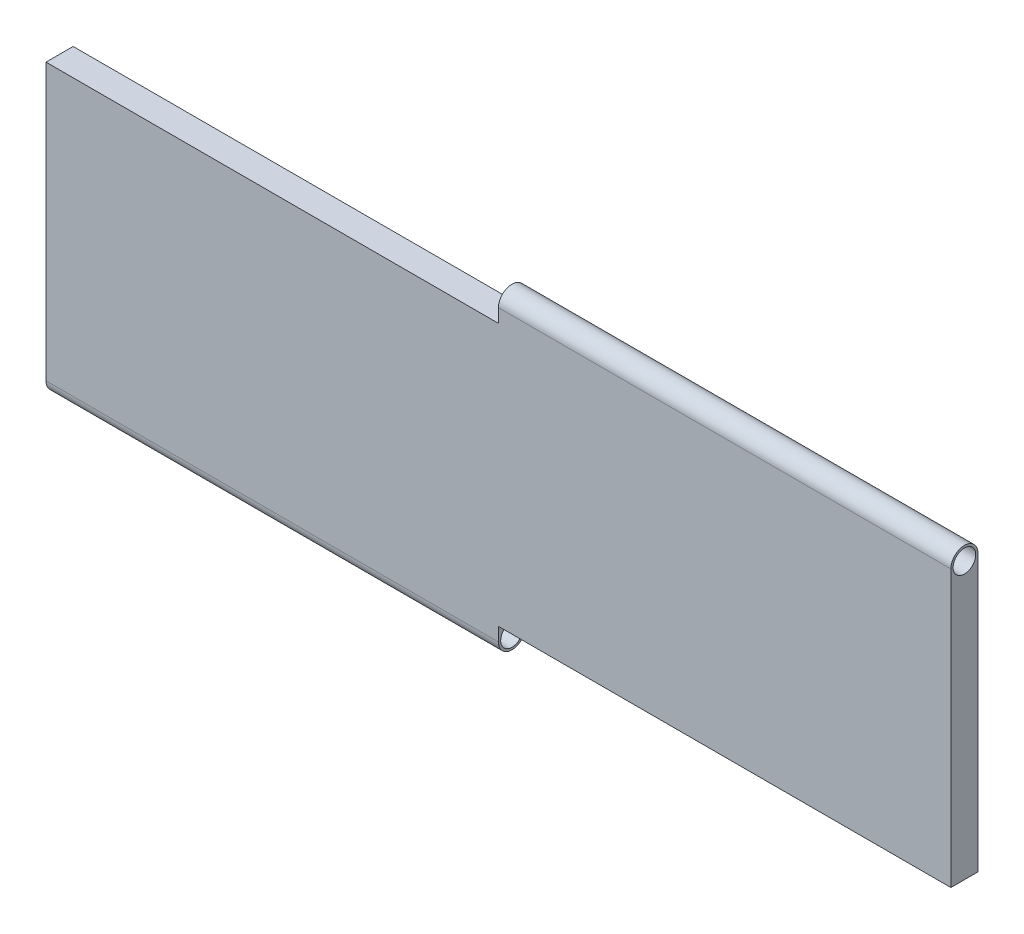
SolidWorks part; units mm, degrees
ref_plane "Front Plane" through (0, 0, 0) normal (0, 0, 1) x (1, 0, 0)
ref_plane "Top Plane" through (0, 0, 0) normal (0, 1, 0) x (1, 0, 0)
ref_plane "Right Plane" through (0, 0, 0) normal (1, 0, 0) x (0, 0, -1)
sketch "Sketch1" plane through (0, 0, 0) normal (0, 0, 1) x (1, 0, 0)
  line L1 (-500, 145) -> (500, 145)
  line L2 (-500, 145) -> (-500, -145)
  line L3 (-500, -145) -> (500, -145)
  line L4 (500, 145) -> (500, -145)
  line L5 (-500, 145) -> (500, -145) construction
  line L6 (-500, -145) -> (500, 145) construction
  point P0 (0, 0)
  dimension "D1" = 1000
  dimension "D2" = 290
extrude "Boss-Extrude1" add sketch "Sketch1" along normal blind 30
sketch "Sketch2" plane through (500, 0, 0) normal (1, 0, 0) x (0, 0, -1)
  line L0 (-30, 145) -> (0, 145) construction
  line L1 (0, 160) -> (0, 145)
  line L2 (-30, 160) -> (-30, 145)
  circle A0 centre (-15, 160) radius 15
  circle A1 centre (-15, 160) radius 12.5
  point P5 (-15, 145)
  line M2 (0, 145) -> (-30, 145)
  dimension "D1" = 30
  dimension "D2" = 25
extrude "Boss-Extrude2" add sketch "Sketch2" against normal blind 500 contours A0 A1 | A0 L2 M2 | A0 L1 M2
sketch "Sketch3" plane through (-500, 0, 0) normal (-1, 0, 0) x (0, 0, 1)
  line L0 (30, -145) -> (0, -145) construction
  line L1 (30, -160) -> (30, -145)
  line L2 (0, -160) -> (0, -145)
  circle A0 centre (15, -160) radius 15
  circle A1 centre (15, -160) radius 12.5
  point P4 (15, -145)
  line M2 (0, -145) -> (30, -145)
  dimension "D1" = 30
  dimension "D2" = 25
extrude "Boss-Extrude3" add sketch "Sketch3" against normal blind 500 contours A0 L2 M2 | A0 A1 | A0 L1 M2
